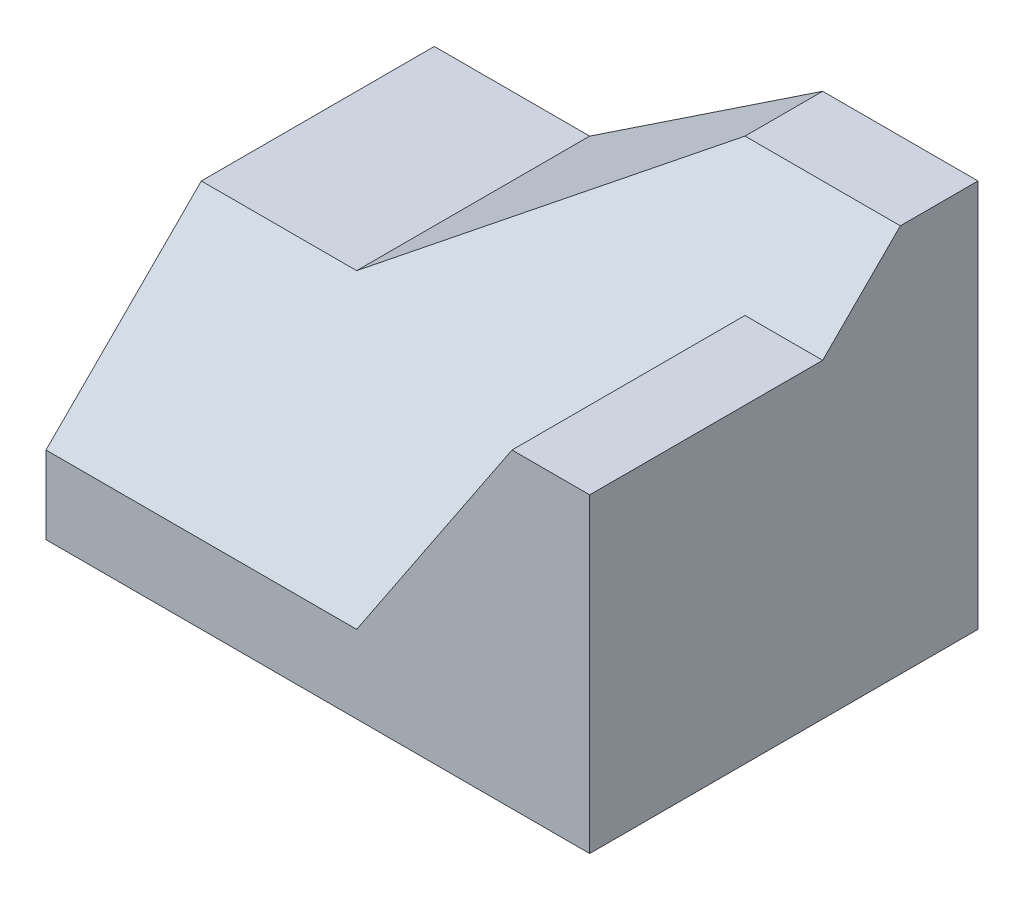
SolidWorks part; units mm, degrees
ref_plane "Front Plane" through (0, 0, 0) normal (0, 0, 1) x (1, 0, 0)
ref_plane "Top Plane" through (0, 0, 0) normal (0, 1, 0) x (1, 0, 0)
ref_plane "Right Plane" through (0, 0, 0) normal (1, 0, 0) x (0, 0, -1)
sketch "Sketch1" plane through (0, 0, 0) normal (0, 0, 1) x (1, 0, 0)
  line L1 (0, 0) -> (70, 0)
  line L2 (0, 0) -> (0, 50)
  line L3 (0, 50) -> (70, 50)
  line L4 (70, 0) -> (70, 50)
  dimension "D1" = 70
  dimension "D2" = 50
extrude "Boss-Extrude1" add sketch "Sketch1" along normal blind 50
sketch "Sketch2" plane through (0, 0, 50) normal (0, 0, 1) x (1, 0, 0)
  line L0 (0, 30) -> (20, 30)
  line L1 (0, 50) -> (0, 0) construction
  line L2 (20, 30) -> (50, 50)
  line L3 (70, 50) -> (0, 50) construction
  line L4 (50, 50) -> (0, 50)
  line L5 (0, 50) -> (0, 30)
  dimension "D1" = 20
  dimension "D2" = 20
  dimension "D3" = 20
extrude "Cut-Extrude1" cut sketch "Sketch2" against normal blind 50
sketch "Sketch3" plane through (70, 0, 0) normal (1, 0, 0) x (0, 0, -1)
  line L0 (-50, 40) -> (-20, 40)
  line L1 (-50, 0) -> (-50, 50) construction
  line L2 (-20, 40) -> (-10, 50)
  line L3 (-50, 50) -> (0, 50) construction
  line L4 (-10, 50) -> (-50, 50)
  line L5 (-50, 50) -> (-50, 40)
  dimension "D1" = 10
  dimension "D2" = 10
  dimension "D3" = 30
extrude "Cut-Extrude2" cut sketch "Sketch3" against normal blind 50
sketch "Sketch4" plane through (0, 0, 50) normal (0, 0, 1) x (1, 0, 0)
  line L0 (70, 40) -> (60, 40)
  line L1 (35, 40) -> (70, 40) construction
  line L2 (60, 40) -> (40, 10)
  line L3 (40, 10) -> (0, 10)
  line L4 (0, 30) -> (0, 0) construction
  line L5 (0, 10) -> (0, 30)
  line L6 (0, 30) -> (20, 30)
  line L7 (20, 30) -> (35, 40)
  line L8 (35, 40) -> (60, 40)
  line M2 (70, 40) -> (35, 40)
  line M3 (35, 40) -> (20, 30)
  line M4 (20, 30) -> (0, 30)
  line M5 (0, 30) -> (0, 0)
  dimension "D1" = 10
  dimension "D2" = 20
  dimension "D3" = 30
extrude "Cut-Extrude3" cut sketch "Sketch4" against normal blind 30 contours L3 L2 M2 M3 M4 M5
ref_plane "Plane1" through (0, 30, 30) normal (0, -0.7071, -0.7071) x (-1, 0, 0)
sketch "Sketch5" plane through (0, 30, 30) normal (0, -0.7071, -0.7071) x (-1, 0, 0)
  line L0 (-70, 28.2843) -> (-40, -28.2843)
  line L1 (-40, -28.2843) -> (0, -28.2843)
  line L2 (0, -28.2843) -> (0, 0)
  line L3 (0, 0) -> (-50, 28.2843)
  line L4 (-50, 28.2843) -> (-70, 28.2843)
extrude "Boss-Extrude2" add sketch "Sketch5" along normal blind 30
sketch "Sketch6" plane through (0, 0, 0) normal (0, 0, -1) x (-1, 0, 0)
  line L0 (-50, 50) -> (-20, 30)
  line L1 (-20, 30) -> (0, 30)
  line L2 (0, 30) -> (0, 60)
  line L3 (0, 60) -> (-50, 60)
  line L4 (-50, 60) -> (-50, 50)
  dimension "D1" = 30
extrude "Cut-Extrude4" cut sketch "Sketch6" against normal blind 54
sketch "Sketch7" plane through (0, 0, 0) normal (0, -1, 0) x (1, 0, 0)
  line L1 (0, 50) -> (70, 50)
  line L2 (0, 50) -> (0, 0)
  line L3 (0, 0) -> (70, 0)
  line L4 (70, 50) -> (70, 0)
extrude "Cut-Extrude5" cut sketch "Sketch7" along normal blind 54
sketch "Sketch8" plane through (0, 0, 0) normal (0, 0, -1) x (-1, 0, 0)
  line L1 (-70, 0) -> (0, 0)
  line L2 (-70, 0) -> (-70, 49.9972)
  line L3 (-70, 49.9972) -> (0, 49.9972)
  line L4 (0, 0) -> (0, 49.9972)
  dimension "D1" = 49.9972
  dimension "D2" = 70
extrude "Cut-Extrude6" cut sketch "Sketch8" along normal blind 54
sketch "Sketch9" plane through (0, 30, 0) normal (0, 1, 0) x (1, 0, 0)
  line L0 (0, -20) -> (12.5, -20)
  line L1 (12.5, -20) -> (0, -30)
  line L2 (0, -30) -> (0, -20)
  line L3 (0, -20) -> (0.4379, -20.1385)
extrude "Boss-Extrude3" add sketch "Sketch9" against normal blind 30
